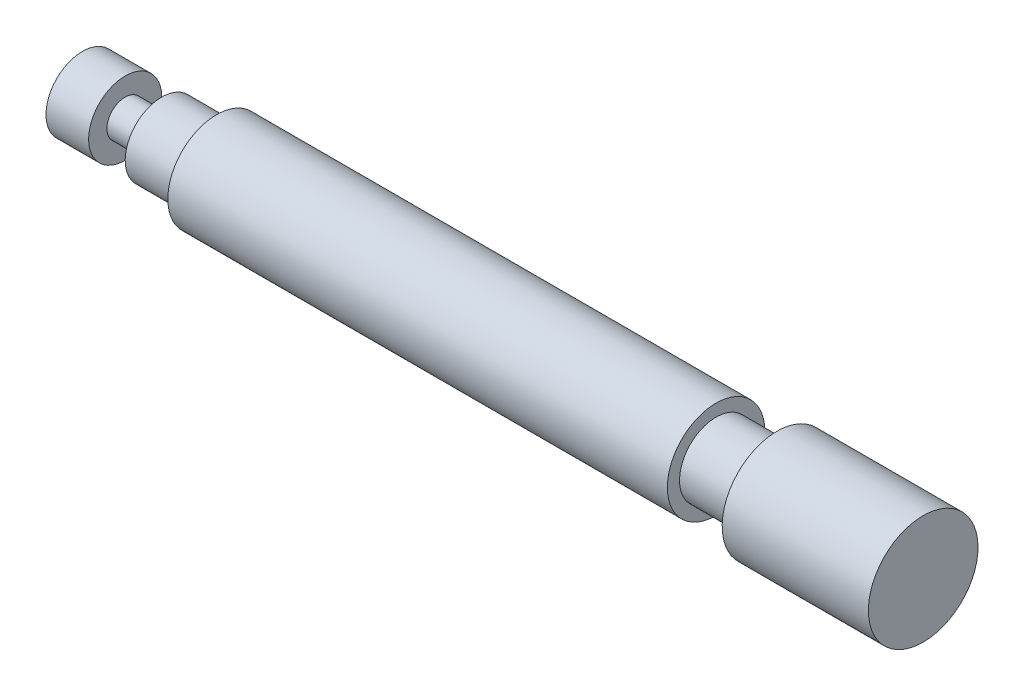
SolidWorks part; units mm, degrees
ref_plane "Front Plane" through (0, 0, 0) normal (0, 0, 1) x (1, 0, 0)
ref_plane "Top Plane" through (0, 0, 0) normal (0, 1, 0) x (1, 0, 0)
ref_plane "Right Plane" through (0, 0, 0) normal (1, 0, 0) x (0, 0, -1)
sketch "Sketch1" plane through (0, 0, 0) normal (0, 0, 1) x (1, 0, 0)
  line L0 (-69, 0) -> (69, 0)
  line L1 (-69, 0) -> (-69, 6)
  line L2 (-69, 6) -> (-62, 6)
  line L3 (-62, 6) -> (-62, 3)
  line L4 (-62, 3) -> (-56, 3)
  line L5 (-56, 3) -> (-56, 6)
  line L6 (-56, 6) -> (-47, 6)
  line L7 (-47, 6) -> (-47, 8)
  line L8 (-47, 8) -> (35, 8)
  line L9 (35, 8) -> (35, 6)
  line L10 (69, 0) -> (69, 9)
  line L11 (69, 9) -> (45, 9)
  line L13 (45, 6) -> (35, 6)
  line L14 (45, 6) -> (45, 9)
  point P4 (0, 0)
  dimension "D1" = 6
  dimension "D2" = 3
  dimension "D3" = 10
  dimension "D4" = 82
  dimension "D5" = 24
  dimension "D6" = 138
  dimension "D7" = 9
  dimension "D8" = 6
  dimension "D9" = 7
revolve "Revolve1" add sketch "Sketch1" angle 360 about L0
